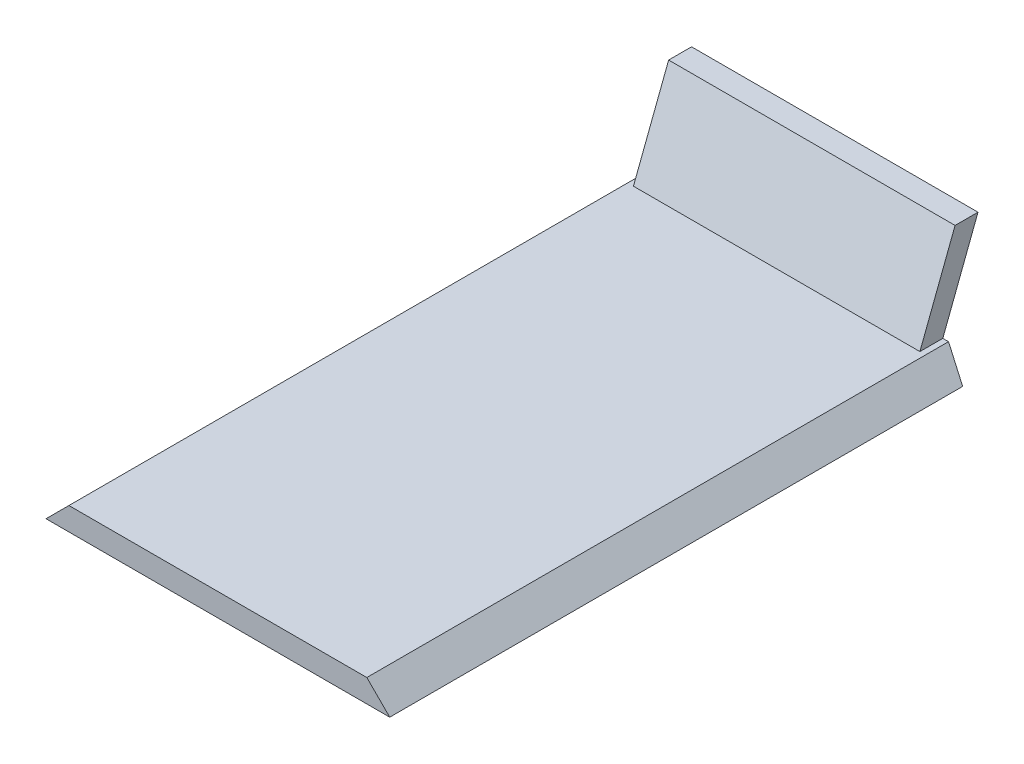
SolidWorks part; units mm, degrees
ref_plane "Front Plane" through (0, 0, 0) normal (0, 0, 1) x (1, 0, 0)
ref_plane "Top Plane" through (0, 0, 0) normal (0, 1, 0) x (1, 0, 0)
ref_plane "Right Plane" through (0, 0, 0) normal (1, 0, 0) x (0, 0, -1)
sketch "Sketch1" plane through (0, 0, 0) normal (0, 0, 1) x (1, 0, 0)
  line L0 (-38.1, 0) -> (38.1, 0)
  line L1 (38.1, 0) -> (33.02, 5.08)
  line L2 (33.02, 5.08) -> (-33.02, 5.08)
  line L3 (-33.02, 5.08) -> (-38.1, 0)
  dimension "D1" = 76.2
  dimension "D2" = 45
  dimension "D3" = 45
  dimension "D4" = 5.08
extrude "Boss-Extrude1" add sketch "Sketch1" along normal blind 127 and the other way blind 19.5479
sketch "Sketch3" plane through (0, 0, 0) normal (1, 0, 0) x (0, 0, -1)
  line L0 (0, 0) -> (9.7501, 25.4)
  line L1 (9.7501, 25.4) -> (4.6701, 25.4)
  line L2 (4.6701, 25.4) -> (-5.08, 0)
  line L3 (-5.08, 0) -> (0, 0)
  dimension "D1" = 5.08
  dimension "D2" = 25.4
  dimension "D3" = 69
extrude "Boss-Extrude3" add sketch "Sketch3" along normal mid plane 63.5
ref_plane "Plane3" through (0, 0, 0) normal (0, -0.3584, -0.9336) x (-1, 0, 0)
other "SurfaceCut2"
